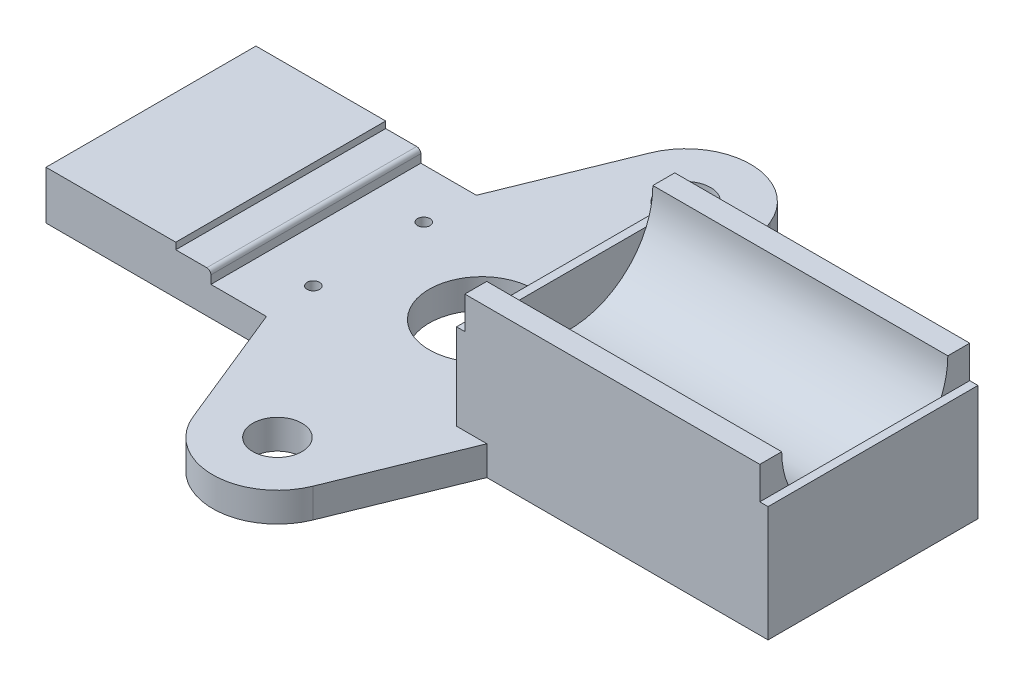
SolidWorks part; units mm, degrees
ref_plane "Front Plane" through (0, 0, 0) normal (0, 0, 1) x (1, 0, 0)
ref_plane "Top Plane" through (0, 0, 0) normal (0, 1, 0) x (1, 0, 0)
ref_plane "Right Plane" through (0, 0, 0) normal (1, 0, 0) x (0, 0, -1)
sketch "Sketch1" plane through (0, 0, 0) normal (0, 1, 0) x (1, 0, 0)
  line L1 (-86.36, 25.4) -> (86.36, 25.4)
  line L2 (-86.36, 25.4) -> (-86.36, -25.4)
  line L3 (-86.36, -25.4) -> (86.36, -25.4)
  line L4 (86.36, 25.4) -> (86.36, -25.4)
  line L5 (-86.36, 25.4) -> (86.36, -25.4) construction
  line L6 (-86.36, -25.4) -> (86.36, 25.4) construction
  point P0 (0, 0)
  dimension "D1" = 172.72
  dimension "D2" = 50.8
extrude "Boss-Extrude1" add sketch "Sketch1" along normal blind 12.7
sketch "Sketch2" plane through (0, 0, 0) normal (0, -1, 0) x (1, 0, 0)
  point P0 (-87.3294, -20.744)
sketch "Sketch4" plane through (86.36, 0, 0) normal (1, 0, 0) x (0, 0, -1)
  line L0 (-25.4, 12.7) -> (-25.4, 35.8)
  line L1 (25.4, 35.8) -> (25.4, 12.7)
  line L2 (-25.4, 35.8) -> (-20.1, 35.8)
  line L3 (25.4, 35.8) -> (20.1, 35.8)
  line L4 (-25.4, 12.7) -> (25.4, 12.7) construction
  line L5 (-25.4, 12.7) -> (25.4, 12.7)
  arc A0 (20.1, 35.8) -> (-20.1, 35.8) centre (0, 35.8) cw
  dimension "D1" = 20.1
  dimension "D2" = 3
extrude "Boss-Extrude2" add sketch "Sketch4" against normal blind 71.374
sketch "Sketch5" plane through (86.36, 0, 0) normal (1, 0, 0) x (0, 0, -1)
  line L0 (25.4, 35.8) -> (25.4, 0) construction
  line L1 (-25.4, 0) -> (25.4, 0)
  line L2 (-25.4, 0) -> (-25.4, 27.94)
  line L3 (-25.4, 27.94) -> (25.4, 27.94)
  line L4 (25.4, 0) -> (25.4, 27.94)
  dimension "D1" = 27.94
extrude "Boss-Extrude3" add sketch "Sketch5" along normal blind 2
sketch "Sketch6" plane through (14.986, 0, 0) normal (-1, 0, 0) x (0, 0, 1)
  line L1 (-25.4, 12.7) -> (25.4, 12.7)
  line L2 (-25.4, 12.7) -> (-25.4, 27.94)
  line L3 (-25.4, 27.94) -> (25.4, 27.94)
  line L4 (25.4, 12.7) -> (25.4, 27.94)
extrude "Boss-Extrude4" add sketch "Sketch6" along normal blind 2
sketch "Sketch7" plane through (0, 0, 25.4) normal (0, 0, 1) x (1, 0, 0)
  line L0 (-86.36, 12.7) -> (-86.36, 11.7)
  line L1 (-86.36, 12.7) -> (-86.36, 0) construction
  line L2 (-86.36, 11.7) -> (-54.96, 11.7)
  line L3 (-54.96, 11.7) -> (-54.96, 10.1)
  line L4 (-54.96, 10.1) -> (-46.46, 10.1)
  line L5 (-46.46, 10.1) -> (-46.46, 7.1)
  line L6 (-46.46, 7.1) -> (12.986, 7.1)
  line L7 (12.986, 7.1) -> (12.986, 12.7)
  line L8 (-86.36, 12.7) -> (12.986, 12.7) construction
  line L9 (12.986, 12.7) -> (-86.36, 12.7)
  line L10 (12.986, 12.7) -> (12.986, 27.94) construction
  dimension "D1" = 1
  dimension "D2" = 31.4
  dimension "D3" = 1.6
  dimension "D4" = 8.5
  dimension "D5" = 3
extrude "Cut-Extrude1" cut sketch "Sketch7" against normal through all
fillet "Fillet1" radius 1 1 edges at (-46.46, 10.1, 0)
sketch "Sketch8" plane through (0, 0, 0) normal (0, -1, 0) x (1, 0, 0)
  circle A0 centre (-6.35, 0) radius 12.7
  point P3 (-13.5634, 0)
  point P5 (0, 0)
  dimension "D1" = 25.4
  dimension "D2" = 6.35
extrude "Cut-Extrude2" cut sketch "Sketch8" against normal up to surface (7.1 mm away) contours A0 up to face at (-16.737, 7.1, 0)
sketch "Sketch9" plane through (0, 0, 0) normal (0, 1, 0) x (1, 0, 0)
  line L0 (-33.02, 25.4) -> (-20.875, 55.3088)
  line L1 (-46.46, 25.4) -> (12.986, 25.4) construction
  line L2 (8.175, 55.3088) -> (20.32, 25.4)
  line L3 (14.986, 25.4) -> (86.36, 25.4) construction
  line L4 (20.32, 25.4) -> (-33.02, 25.4)
  line L5 (-19.69, 0) -> (19.69, 0) construction
  line L6 (20.32, -25.4) -> (-33.02, -25.4)
  line L7 (8.175, -55.3088) -> (20.32, -25.4)
  line L8 (-33.02, -25.4) -> (-20.875, -55.3088)
  arc A0 (-20.875, 55.3088) -> (8.175, 55.3088) centre (-6.35, 49.4106) cw
  circle A1 centre (-6.35, 49.4106) radius 5.9563
  circle A2 centre (-6.35, -49.4106) radius 5.9563
  arc A3 (-20.875, -55.3088) -> (8.175, -55.3088) centre (-6.35, -49.4106) ccw
  point P11 (-6.35, 0)
  dimension "D1" = 15.6769
  dimension "D4" = 11.9126
  dimension "D2" = 39.6875
  dimension "D3" = 53.34
extrude "Boss-Extrude5" add sketch "Sketch9" along normal up to surface (7.1 mm away) up to face at (-6.35, 7.1, -12.7)
sketch "Sketch10" plane through (0, 7.1, 0) normal (0, 1, 0) x (1, 0, 0)
  line L0 (-46.46, 25.4) -> (-46.46, -25.4) construction
  line L1 (-46.46, -25.4) -> (-33.02, -25.4) construction
  line L2 (-46.46, 25.4) -> (-33.02, 25.4) construction
  circle A0 centre (-33.76, 13.41) radius 1.5
  circle A1 centre (-33.76, -13.31) radius 1.5
  point P0 (-33.76, 13.41)
  point P1 (-33.76, -13.31)
  point P14 (0, 0)
  dimension "D1" = 3
  dimension "D2" = 12.7
  dimension "D3" = 12.09
  dimension "D4" = 11.99
extrude "Cut-Extrude3" cut sketch "Sketch10" against normal up to surface (7.1 mm away) up to face at (-6.35, 0, -12.7)
